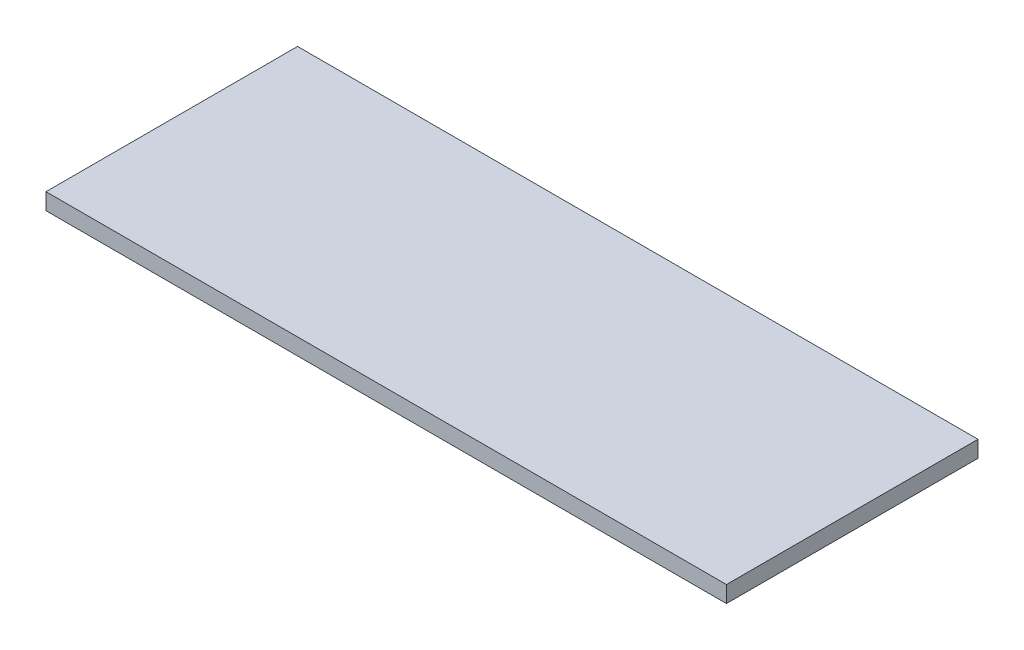
SolidWorks part; units mm, degrees
material "Maple"
ref_plane "Front Plane" through (0, 0, 0) normal (0, 0, 1) x (1, 0, 0)
ref_plane "Top Plane" through (0, 0, 0) normal (0, 1, 0) x (1, 0, 0)
ref_plane "Right Plane" through (0, 0, 0) normal (1, 0, 0) x (0, 0, -1)
sketch "Sketch1" plane through (0, 0, 0) normal (0, 1, 0) x (1, 0, 0)
  line L1 (-82.5, -30.5) -> (82.5, -30.5)
  line L2 (-82.5, -30.5) -> (-82.5, 30.5)
  line L3 (-82.5, 30.5) -> (82.5, 30.5)
  line L4 (82.5, -30.5) -> (82.5, 30.5)
  line L5 (-82.5, -30.5) -> (82.5, 30.5) construction
  line L6 (-82.5, 30.5) -> (82.5, -30.5) construction
  point P0 (0, 0)
  dimension "D1" = 61
  dimension "D2" = 165
extrude "Boss-Extrude1" add sketch "Sketch1" along normal blind 4
